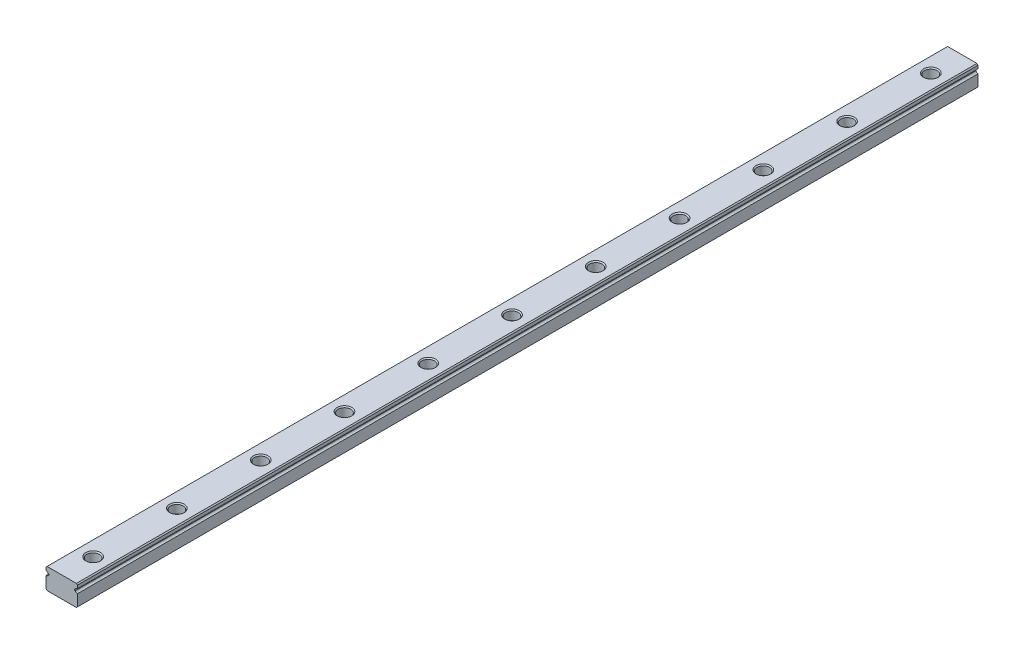
SolidWorks part; units mm, degrees
material "AISI 1035 鋼 (SS)"
ref_plane "Front Plane" through (0, 0, 0) normal (0, 0, 1) x (1, 0, 0)
ref_plane "Top Plane" through (0, 0, 0) normal (0, 1, 0) x (1, 0, 0)
ref_plane "Right Plane" through (0, 0, 0) normal (1, 0, 0) x (0, 0, -1)
sketch "Sketch1" plane through (0, 0, 0) normal (0, 0, 1) x (1, 0, 0)
  line L0 (-7.5, 0) -> (-7.5, 10) construction
  line L1 (-7.5, 10) -> (7.5, 10)
  line L2 (-7.5, 0) -> (7.5, 0)
  line L3 (-7.5, 10) -> (-7.5, 8.25)
  line L4 (-7.5, 8.25) -> (-6.5, 7.25) construction
  line L5 (-6.5, 7.25) -> (-6, 7.25)
  line L6 (-6.5, 6.75) -> (-7.5, 5.75) construction
  line L7 (-7.5, 5.75) -> (-7.5, 0)
  line L8 (-6, 7.25) -> (-6, 6.75)
  line L9 (-6, 6.75) -> (-6.5, 6.75)
  line L10 (-6.5, 6.75) -> (-6.25, 7) construction
  line L11 (-6.25, 7) -> (-6.5, 7.25) construction
  line L12 (-7.5, 8.25) -> (-7.5, 8.0308)
  line L13 (-7.5, 5.75) -> (-7.5, 5.9692)
  line L14 (0, 10) -> (0, 0) construction
  line L15 (6.25, 7) -> (6.5, 7.25) construction
  line L16 (6.5, 6.75) -> (6.25, 7) construction
  line L17 (6.5, 6.75) -> (7.5, 5.75) construction
  line L18 (7.5, 8.25) -> (6.5, 7.25) construction
  line L19 (7.5, 0) -> (7.5, 10) construction
  line L20 (7.5, 5.75) -> (7.5, 5.9692)
  line L21 (7.5, 8.25) -> (7.5, 8.0308)
  line L22 (6, 6.75) -> (6.5, 6.75)
  line L23 (6, 7.25) -> (6, 6.75)
  line L24 (7.5, 5.75) -> (7.5, 0)
  line L25 (6.5, 7.25) -> (6, 7.25)
  line L26 (7.5, 10) -> (7.5, 8.25)
  arc A0 (-7.5, 5.9692) -> (-6.5, 6.75) centre (-7.5, 7) ccw
  arc A1 (-6.5, 7.25) -> (-7.5, 8.0308) centre (-7.5, 7) ccw
  arc A2 (6.5, 7.25) -> (7.5, 8.0308) centre (7.5, 7) cw
  arc A3 (7.5, 5.9692) -> (6.5, 6.75) centre (7.5, 7) cw
  point P4 (-6, 7)
  point P28 (6, 7)
  dimension "D1" = 10
  dimension "D2" = 15
  dimension "D3" = 0.5
  dimension "D4" = 45
  dimension "D5" = 3
  dimension "D6" = 1.5
extrude "Boss-Extrude1" add sketch "Sketch1" along normal blind 430
chamfer "Chamfer1" distance 0.5 angle 45 4 edges at (-7.5, 0, 215) (7.5, 0, 215) (-7.5, 10, 215) (7.5, 10, 215)
hole_wizard "M3 六角承窩頭蓋螺釘的柱孔1" positions "3DSketch1" profile "Sketch3" counterbore size "M3" standard "ISO" end condition through all
sketch3d "3DSketch1"
  line L0 (0, 10, 0) -> (0, 10, 15) construction
  line L1 (7, 10, 0) -> (-7, 10, 0) construction
  point P0 (0, 10, 15)
  dimension "D1" = 15
sketch "Sketch3" plane through (0, 10, 15) normal (1, 0, 0) x (0, 0, 1)
  line L0 (0, 0) -> (0, 10)
  line L1 (1.75, 9.75) -> (2, 10)
  line L2 (3, 4.5) -> (1.75, 4.5)
  line L3 (1.75, 4.5) -> (1.75, 9.75)
  line L5 (3, 4.5) -> (3, 0.5)
  line L6 (3, 0.5) -> (3.5, 0)
  line L7 (3.5, 0) -> (0, 0)
  line L8 (-3, 0.5) -> (-3.5, 0) construction
  line L11 (0, -6.35) -> (0, 107.95) construction
  line L12 (2, 10) -> (0, 10)
  line L13 (-1.75, 9.75) -> (-2, 10) construction
  dimension "Thru Hole Dia." = 3.5
  dimension "Thru Hole Depth" = 10
  dimension "C'Bore Dia." = 6
  dimension "C'Bore Depth" = 4.5
  dimension "Near C'Sink Dia." = 7
  dimension "Near C'Sink Angle" = 90
  dimension "Far C'Sink Dia." = 4
  dimension "Far C'Sink Angle" = 90
pattern_linear "LPattern1" count 11 spacing 40 along (0, 0, 1) of "M3 六角承窩頭蓋螺釘的柱孔1"
